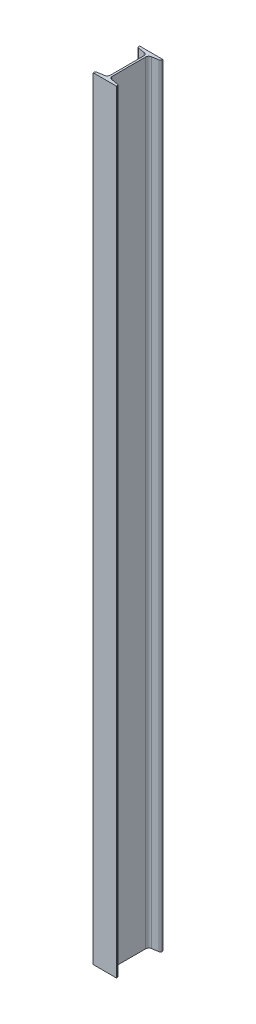
SolidWorks part; units mm, degrees
material "AISI 1020"
ref_plane "Front Plane" through (0, 0, 0) normal (0, 0, 1) x (1, 0, 0)
ref_plane "Top Plane" through (0, 0, 0) normal (0, 1, 0) x (1, 0, 0)
ref_plane "Right Plane" through (0, 0, 0) normal (1, 0, 0) x (0, 0, -1)
sketch "Sketch2" plane through (0, 0, 0) normal (0, 0, 1) x (1, 0, 0)
  line L0 (0, 0) -> (0, 2000)
  dimension "D1" = 2000
other "Sb beam 120 X 12(1)"
ref_plane "Plane1" through (0, 0, 0) normal (0, 1, 0) x (-1, 0, 0)
sketch "Sketch15" plane through (0, 0, 0) normal (0, 1, 0) x (-1, 0, 0)
  line L0 (-30, -60) -> (-30, -58.0801)
  line L1 (-26.6576, -54.1345) -> (-9.1847, -51.2221)
  line L2 (-2.5, -43.331) -> (-2.5, 43.331)
  line L3 (-9.1847, 51.2221) -> (-26.6576, 54.1345)
  line L4 (-30, 58.0801) -> (-30, 60)
  line L5 (-30, 60) -> (30, 60)
  line L6 (30, 60) -> (30, 58.0801)
  line L7 (26.6576, 54.1345) -> (9.1847, 51.2221)
  line L8 (2.5, 43.331) -> (2.5, -43.331)
  line L9 (9.1847, -51.2221) -> (26.6576, -54.1345)
  line L10 (30, -58.0801) -> (30, -60)
  line L11 (30, -60) -> (-30, -60)
  line L15 (-2.5, 0) -> (2.5, 0) construction
  arc A0 (-9.1847, -51.2221) -> (-2.5, -43.331) centre (-10.5, -43.331) ccw
  arc A1 (-2.5, 43.331) -> (-9.1847, 51.2221) centre (-10.5, 43.331) ccw
  arc A2 (9.1847, 51.2221) -> (2.5, 43.331) centre (10.5, 43.331) ccw
  arc A3 (2.5, -43.331) -> (9.1847, -51.2221) centre (10.5, -43.331) ccw
  arc A4 (-26.6576, 54.1345) -> (-30, 58.0801) centre (-26, 58.0801) cw
  arc A5 (26.6576, 54.1345) -> (30, 58.0801) centre (26, 58.0801) ccw
  arc A6 (-30, -58.0801) -> (-26.6576, -54.1345) centre (-26, -58.0801) cw
  arc A7 (30, -58.0801) -> (26.6576, -54.1345) centre (26, -58.0801) ccw
  point P1 (0, 60)
  point P8 (0, -60)
  point P21 (0, 0)
  point P34 (0, 0)
  dimension "RI" = 8
  dimension "D3" = 4
  dimension "BF" = 60
  dimension "D2" = 9.463
  dimension "DEPTH" = 120
  dimension "TW" = 5
  dimension "D1" = 86.662
